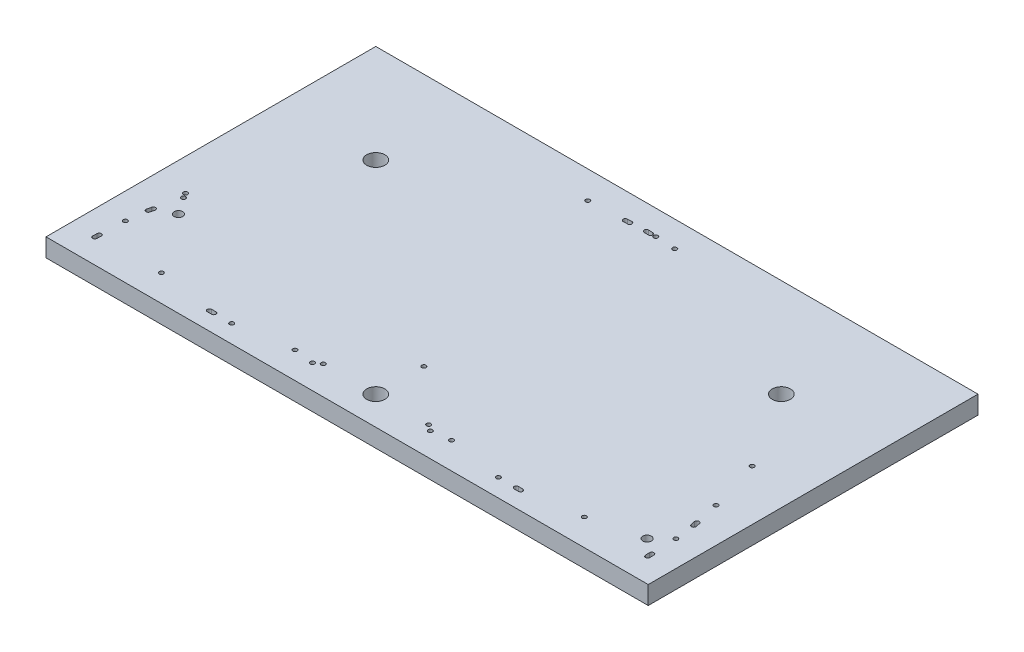
SolidWorks part; units mm, degrees
ref_plane "Front Plane" through (0, 0, 0) normal (0, 0, 1) x (1, 0, 0)
ref_plane "Top Plane" through (0, 0, 0) normal (0, 1, 0) x (1, 0, 0)
ref_plane "Right Plane" through (0, 0, 0) normal (1, 0, 0) x (0, 0, -1)
sketch "Sketch1" plane through (0, 0, 0) normal (0, 1, 0) x (1, 0, 0)
  line L0 (212.5, 0) -> (212.5, 230) construction
  line L1 (0, 0) -> (420, 0)
  line L2 (0, 0) -> (0, 230)
  line L3 (0, 230) -> (420, 230)
  line L4 (420, 0) -> (420, 230)
extrude "Boss-Extrude1" add sketch "Sketch1" along normal blind 12.7
sketch "Sketch3" plane through (0, 12.7, 0) normal (0, 1, 0) x (-1, 0, 0)
  line L0 (-210, 0) -> (-210, -230) construction
sketch "Sketch7" plane through (196.4605, 12.7, -62.603) normal (0, 1, 0) x (0.0903, 0, 0.9959)
  line L4 (60.9136, 117.0192) -> (60.6428, 114.0315) construction
  line L5 (62.4075, 116.8838) -> (62.1367, 113.8961)
  line L6 (59.4197, 117.1546) -> (59.149, 114.1668)
  line L7 (41.3276, -99.0951) -> (41.5983, -96.1073) construction
  line L8 (39.8337, -98.9597) -> (40.1045, -95.9719)
  line L9 (42.8214, -99.2305) -> (43.0922, -96.2427)
  line L10 (29.4308, 201.9279) -> (26.4565, 201.5363) construction
  line L11 (29.6266, 200.4408) -> (26.6523, 200.0492)
  line L12 (29.235, 203.4151) -> (26.2607, 203.0235)
  line L13 (-148.6979, 23.0202) -> (-148.3193, 25.9963) construction
  line L14 (-150.1859, 23.2095) -> (-149.8073, 26.1856)
  line L15 (-147.2099, 22.8309) -> (-146.8313, 25.807)
  line L16 (29.4308, -182.6499) -> (26.4565, -182.2583) construction
  line L17 (29.235, -184.1371) -> (26.2607, -183.7455)
  line L18 (29.6266, -181.1628) -> (26.6523, -180.7712)
  line L21 (64.2321, 201.3494) -> (61.236, 201.5031) construction
  line L22 (64.1552, 199.8514) -> (61.1592, 200.005)
  line L23 (64.3089, 202.8474) -> (61.3129, 203.0011)
  line L24 (-149.1576, 9.0884) -> (-149.0039, 12.0844) construction
  line L25 (-150.6556, 9.1652) -> (-150.5019, 12.1613)
  line L26 (-147.6595, 9.0115) -> (-147.5059, 12.0076)
  line L27 (-4.9072, -176.9604) -> (-7.7627, -176.0405) construction
  line L28 (-5.3671, -178.3881) -> (-8.2226, -177.4682)
  line L29 (-4.4472, -175.5327) -> (-7.3027, -174.6127)
  circle A0 centre (43.6512, 9.639) radius 6.35
  circle A1 centre (-109.9574, -118.4407) radius 6.35
  circle A2 centre (43.0997, -31.5081) radius 1.5
  circle A3 centre (9.1062, -179.9741) radius 1.5
  arc A4 (62.4075, 116.8838) -> (59.4197, 117.1546) centre (60.9136, 117.0192) ccw
  circle A5 centre (42.7266, -83.6583) radius 1.5
  circle A6 centre (59.5146, 101.5825) radius 1.5
  arc A7 (39.8337, -98.9597) -> (42.8214, -99.2305) centre (41.3276, -99.0951) ccw
  arc A8 (59.149, 114.1668) -> (62.1367, 113.8961) centre (60.6428, 114.0315) ccw
  circle A9 centre (9.1062, 199.2521) radius 1.5
  circle A10 centre (-146.1109, 43.3563) radius 1.5
  circle A11 centre (46.9861, 46.3699) radius 1.5
  circle A12 centre (31.779, -137.979) radius 1.5
  circle A13 centre (40.196, -45.105) radius 1.5
  circle A14 centre (50.0404, 63.5195) radius 1.5
  circle A15 centre (58.4046, 155.8101) radius 1.5
  circle A16 centre (10.2879, 12.6627) radius 1.5
  circle A17 centre (40.3591, -26.8593) radius 1.5
  circle A18 centre (50.5266, 50.3711) radius 1.5
  circle A20 centre (-84.4285, 163.2476) radius 6.35
  circle A21 centre (-27.9998, 191.5356) radius 1.5
  circle A22 centre (-150.1763, -15.8789) radius 1.5
  circle A23 centre (-27.9998, -172.2576) radius 1.5
  circle A24 centre (-12.1575, -163.5932) radius 3
  circle A25 centre (52.7225, 191.4128) radius 3
  arc A26 (43.0922, -96.2427) -> (40.1045, -95.9719) centre (41.5983, -96.1073) ccw
  arc A27 (29.6266, 200.4408) -> (29.235, 203.4151) centre (29.4308, 201.9279) ccw
  arc A28 (26.2607, 203.0235) -> (26.6523, 200.0492) centre (26.4565, 201.5363) ccw
  arc A29 (-150.1859, 23.2095) -> (-147.2099, 22.8309) centre (-148.6979, 23.0202) ccw
  arc A30 (-146.8313, 25.807) -> (-149.8073, 26.1856) centre (-148.3193, 25.9963) ccw
  arc A31 (29.235, -184.1371) -> (29.6266, -181.1628) centre (29.4308, -182.6499) ccw
  arc A32 (26.6523, -180.7712) -> (26.2607, -183.7455) centre (26.4565, -182.2583) ccw
  circle A34 centre (-24.4196, -170.6742) radius 1.5
  circle A35 centre (-148.0509, 29.5585) radius 1.5
  circle A37 centre (43.7577, 202.3732) radius 1.5
  arc A39 (64.1552, 199.8514) -> (64.3089, 202.8474) centre (64.2321, 201.3494) ccw
  arc A40 (61.3129, 203.0011) -> (61.1592, 200.005) centre (61.236, 201.5031) ccw
  arc A41 (-150.6556, 9.1652) -> (-147.6595, 9.0115) centre (-149.1576, 9.0884) ccw
  arc A42 (-147.5059, 12.0076) -> (-150.5019, 12.1613) centre (-149.0039, 12.0844) ccw
  arc A43 (-5.3671, -178.3881) -> (-4.4472, -175.5327) centre (-4.9072, -176.9604) ccw
  arc A44 (-7.3027, -174.6127) -> (-8.2226, -177.4682) centre (-7.7627, -176.0405) ccw
  point P17 (60.7782, 115.5253)
  point P64 (41.463, -97.6012)
  point P71 (27.9436, 201.7321)
  point P78 (-148.5086, 24.5083)
  point P85 (27.9436, -182.4541)
  point P108 (62.734, 201.4262)
  point P115 (-149.0807, 10.5864)
  point P122 (-6.3349, -176.5004)
extrude "Cut-Extrude1" cut sketch "Sketch7" against normal blind 12.7
